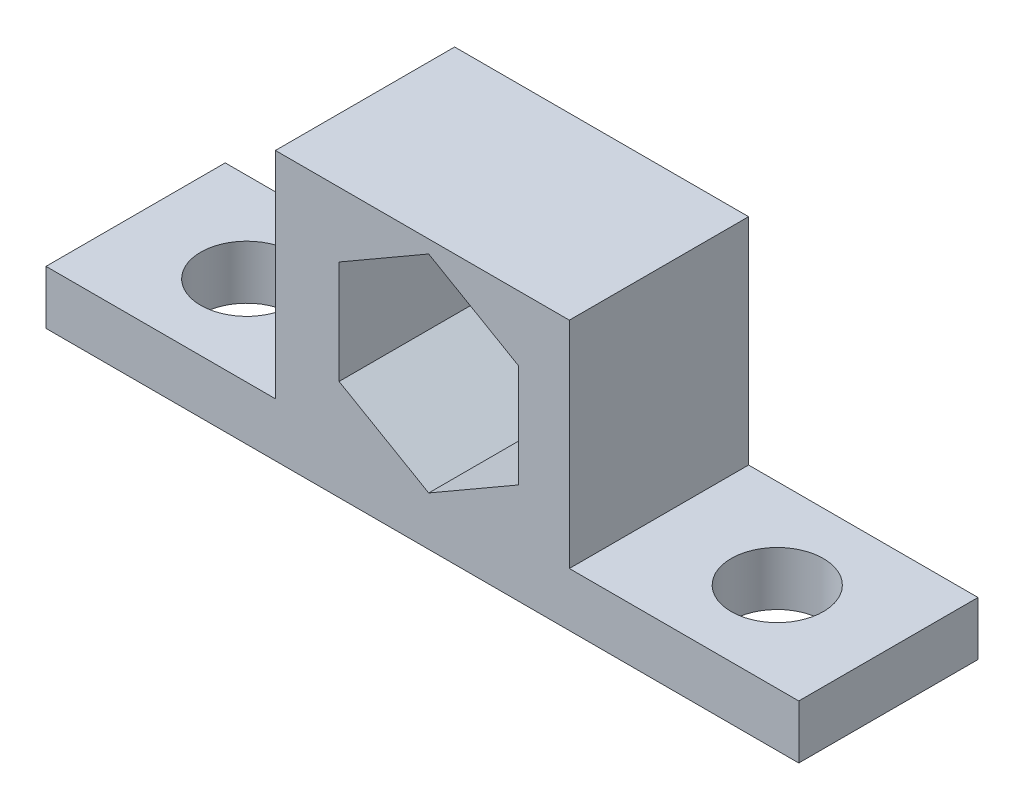
SolidWorks part; units mm, degrees
ref_plane "Front Plane" through (0, 0, 0) normal (0, 0, 1) x (1, 0, 0)
ref_plane "Top Plane" through (0, 0, 0) normal (0, 1, 0) x (1, 0, 0)
ref_plane "Right Plane" through (0, 0, 0) normal (1, 0, 0) x (0, 0, -1)
sketch "Sketch1" plane through (0, 0, 0) normal (0, 1, 0) x (1, 0, 0)
  line L1 (-35.381, 3.1139) -> (17.959, 3.1139)
  line L2 (-35.381, 3.1139) -> (-35.381, -9.5861)
  line L3 (-35.381, -9.5861) -> (17.959, -9.5861)
  line L4 (17.959, 3.1139) -> (17.959, -9.5861)
  line L5 (-19.887, 3.1139) -> (2.465, 3.1139)
  line L6 (-19.887, 3.1139) -> (-19.887, -9.5861)
  line L7 (-19.887, -9.5861) -> (2.465, -9.5861)
  line L8 (2.465, 3.1139) -> (2.465, -9.5861)
  circle A0 centre (-27.507, -3.2361) radius 3.2639
  circle A1 centre (10.085, -3.2361) radius 3.2639
  dimension "D7" = 6.5278
  dimension "D8" = 6.5278
  dimension "D1" = 12.7
  dimension "D2" = 53.34
  dimension "D3" = 7.874
  dimension "D4" = 7.874
  dimension "D5" = 6.35
  dimension "D6" = 6.35
  dimension "D9" = 7.62
  dimension "D10" = 7.62
extrude "Boss-Extrude3" add sketch "Sketch1" along normal blind 3.81 contours L6 L1 L2 L3 A0 | L8 L1 L6 L3 | L1 L8 L3 L4 A1
sketch "Sketch3" plane through (0, 3.81, 0) normal (0, 1, 0) x (1, 0, 0)
  line L0 (-35.381, -9.5861) -> (17.959, -9.5861) construction
  line L1 (-19.125, -9.5861) -> (1.703, -9.5861)
  line L2 (-19.125, -9.5861) -> (-19.125, 3.1139)
  line L3 (-19.125, 3.1139) -> (1.703, 3.1139)
  line L4 (1.703, -9.5861) -> (1.703, 3.1139)
  line L5 (-35.381, 3.1139) -> (17.959, 3.1139) construction
  circle A0 centre (-27.507, -3.2361) radius 3.2639 construction
  circle A1 centre (10.085, -3.2361) radius 3.2639 construction
  dimension "D1" = 8.382
  dimension "D2" = 8.382
extrude "Boss-Extrude4" add sketch "Sketch3" along normal blind 15.24
sketch "Sketch4" plane through (0, 0, 9.5861) normal (0, 0, 1) x (1, 0, 0)
  line L2 (-8.2628, 18.1273) -> (-14.6128, 14.4612)
  line L3 (-14.6128, 14.4612) -> (-14.6128, 7.1288)
  line L4 (-14.6128, 7.1288) -> (-8.2628, 3.4627)
  line L5 (-8.2628, 3.4627) -> (-1.9128, 7.1288)
  line L6 (-1.9128, 7.1288) -> (-1.9128, 14.4612)
  line L7 (-1.9128, 14.4612) -> (-8.2628, 18.1273)
  dimension "D3" = 12.7
extrude "Cut-Extrude2" cut sketch "Sketch4" against normal up to next
